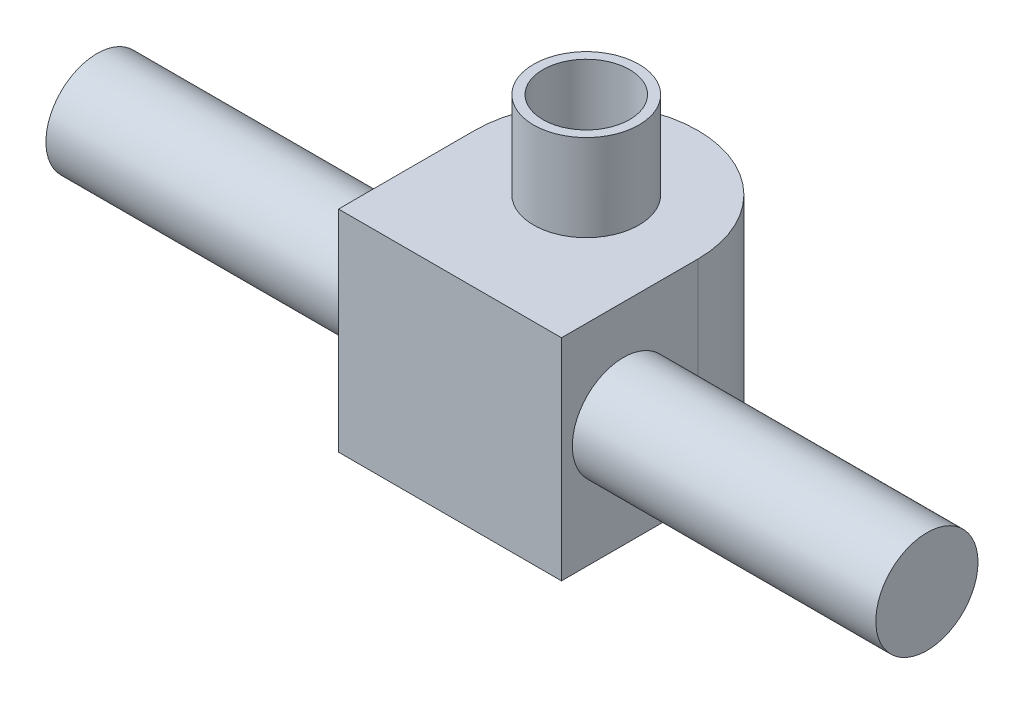
SolidWorks part; units mm, degrees
ref_plane "Front Plane" through (0, 0, 0) normal (0, 0, 1) x (1, 0, 0)
ref_plane "Top Plane" through (0, 0, 0) normal (0, 1, 0) x (1, 0, 0)
ref_plane "Right Plane" through (0, 0, 0) normal (1, 0, 0) x (0, 0, -1)
sketch "Sketch1" plane through (0, 0, 0) normal (0, 1, 0) x (1, 0, 0)
  circle A0 centre (0, 0) radius 8.5
  circle A1 centre (0, 0) radius 7
  dimension "D1" = 17
  dimension "D2" = 14
extrude "Boss-Extrude1" add sketch "Sketch1" along normal blind 48
sketch "Sketch2" plane through (0, 0, 0) normal (0, -1, 0) x (1, 0, 0)
  line L0 (-18, 22) -> (18, 22)
  line L1 (18, 22) -> (18, 0)
  line L2 (0, 22) -> (0, -18) construction
  line L3 (0, 0) -> (18, 0) construction
  line L4 (-18, 22) -> (-18, 0)
  arc A0 (18, 0) -> (-18, 0) centre (0, 0) cw
  circle A1 centre (0, 0) radius 7 construction
  circle A2 centre (0, 0) radius 8.5
  circle A3 centre (0, 0) radius 8.5 construction
  dimension "D1" = 11
  dimension "D2" = 22
extrude "Boss-Extrude2" add sketch "Sketch2" against normal blind 34
sketch "Sketch3" plane through (0, 0, 0) normal (0, -1, 0) x (1, 0, 0)
  line L0 (0, 0) -> (0, -18) construction
  arc A0 (-18, 0) -> (18, 0) centre (0, 0) ccw construction
  circle A1 centre (0, -15.5) radius 1.5
  circle A2 centre (0, 0) radius 7 construction
  circle A3 centre (-15.5, 0) radius 1.5
  circle A4 centre (0, 15.5) radius 1.5
  circle A5 centre (15.5, 0) radius 1.5
  point P19 (0, 0)
  dimension "D1" = 15.5
  dimension "D2" = 3
  dimension "D3" = 4
extrude "Cut-Extrude1" cut sketch "Sketch3" against normal blind 10
sketch "Sketch4" plane through (0, 0, 0) normal (1, 0, 0) x (0, 0, -1)
  line L0 (-22, 34) -> (-22, 0) construction
  line L1 (19.8, 0) -> (-19.8, 0) construction
  circle A0 centre (-12, 18) radius 8.25
  dimension "D1" = 16.5
  dimension "D2" = 10
  dimension "D3" = 18
extrude "Boss-Extrude3" add sketch "Sketch4" along normal blind 67 and the other way blind 67
